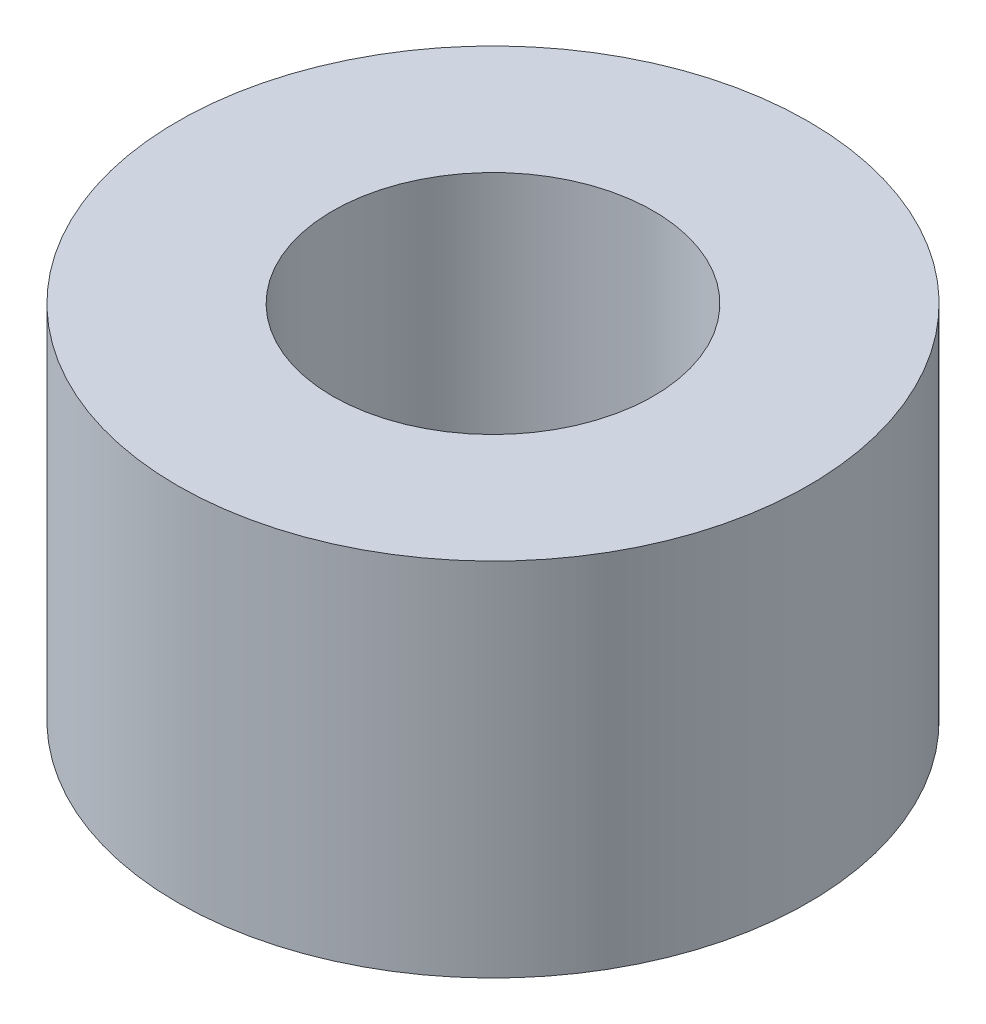
SolidWorks part; units mm, degrees
ref_plane "Front Plane" through (0, 0, 0) normal (0, 0, 1) x (1, 0, 0)
ref_plane "Top Plane" through (0, 0, 0) normal (0, 1, 0) x (1, 0, 0)
ref_plane "Right Plane" through (0, 0, 0) normal (1, 0, 0) x (0, 0, -1)
sketch "Sketch1" plane through (0, 0, 0) normal (0, 1, 0) x (1, 0, 0)
  circle A0 centre (0, 0) radius 6.242
  dimension "D1" = 12.4841
extrude "Boss-Extrude1" add sketch "Sketch1" along normal blind 7.145
sketch "Sketch2" plane through (0, 0, 0) normal (0, 1, 0) x (1, 0, 0)
  circle A0 centre (0, 0) radius 3.175
  dimension "D1" = 6.35
extrude "Cut-Extrude1" cut sketch "Sketch2" along normal through all
